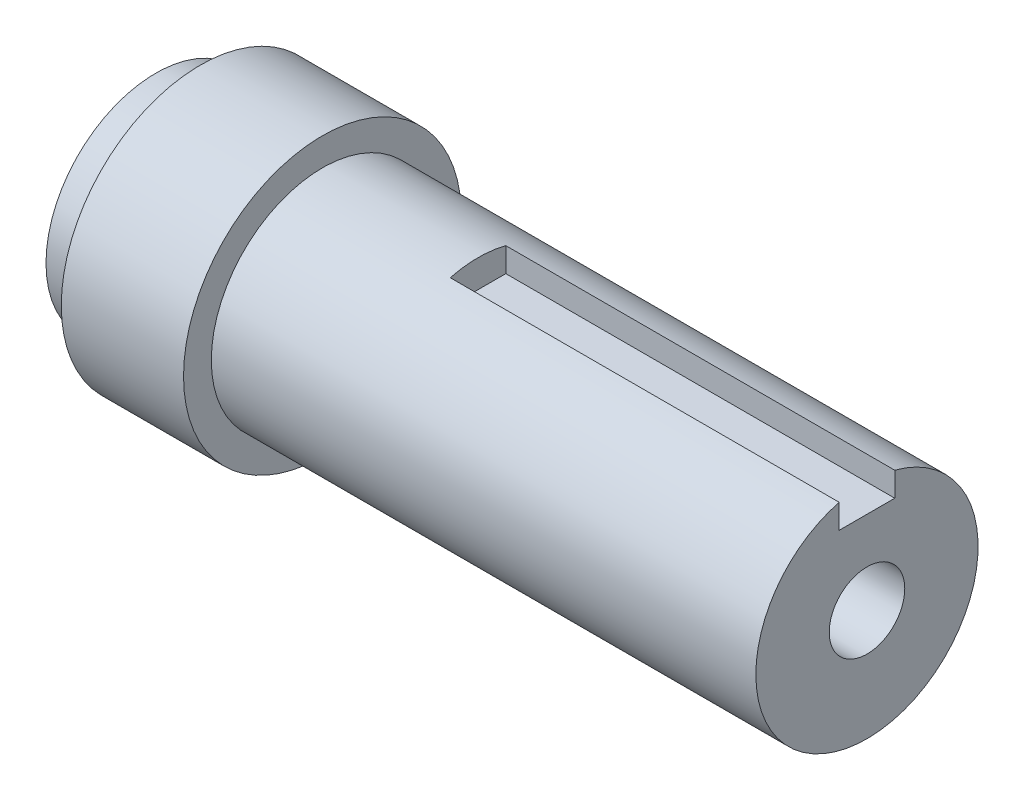
SolidWorks part; units mm, degrees
material "AISI 1020"
ref_plane "Спереди" through (0, 0, 0) normal (0, 0, 1) x (1, 0, 0)
ref_plane "Сверху" through (0, 0, 0) normal (0, 1, 0) x (1, 0, 0)
ref_plane "Справа" through (0, 0, 0) normal (1, 0, 0) x (0, 0, -1)
sketch "Эскиз1" plane through (0, 0, 0) normal (0, 1, 0) x (1, 0, 0)
  line L0 (-1000, 0) -> (49000, 0) construction
  line L1 (0, 0) -> (0, 9.875)
  line L2 (0, 9.875) -> (4, 9.875)
  line L3 (4, -0.25) -> (4, 20) construction
  line L4 (4, 9.875) -> (4, 12.5)
  line L5 (4, 12.5) -> (15, 12.5)
  line L6 (15, 15) -> (15, -15) construction
  line L7 (15, 12.5) -> (15, 10)
  line L8 (15, 22) -> (15, -22) construction
  line L9 (15, 10) -> (64, 10)
  line L10 (64, 10) -> (64, 0)
  line L11 (27.5, 10) -> (16.5, 10) construction
  line L13 (0, 0) -> (64, 0)
  line L14 (61, 12.5) -> (61, 385.4467) construction
  point P20 (0, 0)
  point P21 (0, 0)
  dimension "D1" = 3
  dimension "25" = 25
revolve "Повернуть1" add sketch "Эскиз1" angle 360 about L0
sketch "Эскиз2" plane through (64, 0, 0) normal (1, 0, 0) x (0, 0, -1)
  line L1 (-2.5, 12.5) -> (2.5, 12.5)
  line L2 (-2.5, 12.5) -> (-2.5, 7.5)
  line L3 (-2.5, 7.5) -> (2.5, 7.5)
  line L4 (2.5, 12.5) -> (2.5, 7.5)
  line L5 (-2.5, 12.5) -> (2.5, 7.5) construction
  line L6 (-2.5, 7.5) -> (2.5, 12.5) construction
  circle A0 centre (0, 0) radius 10 construction
  point P0 (0, 10)
  dimension "D1" = 5
extrude "Вырез-Вытянуть1" cut sketch "Эскиз2" against normal up to surface (35 mm away)
hole_wizard "Отверстие обработанное метчиком M81" positions "Эскиз3" profile "Эскиз4" tap size "M8" standard "ISO"
sketch "Эскиз3" plane through (64, 0, 0) normal (1, 0, 0) x (0, 0, -1)
  point P0 (0, 0)
sketch "Эскиз4" plane through (64, 0, 0) normal (0, 1, 0) x (0, 0, -1)
  line L0 (0, 0) -> (0, 27.0429)
  line L1 (0, 27.0429) -> (3.4, 25)
  line L2 (3.4, 25) -> (3.4, 0)
  line L5 (3.4, 0) -> (0, 0)
  line L10 (0, 27.0429) -> (-3.4, 25) construction
  line L11 (0, -6.35) -> (0, 107.95) construction
  dimension "Диаметр сверла" = 6.8
  dimension "Глубина сверла" = 25
  dimension "Угол заточки сверла" = 118
cosmetic thread "Отверстие резьбы1" parameters "D1"=20, "D2"=8
